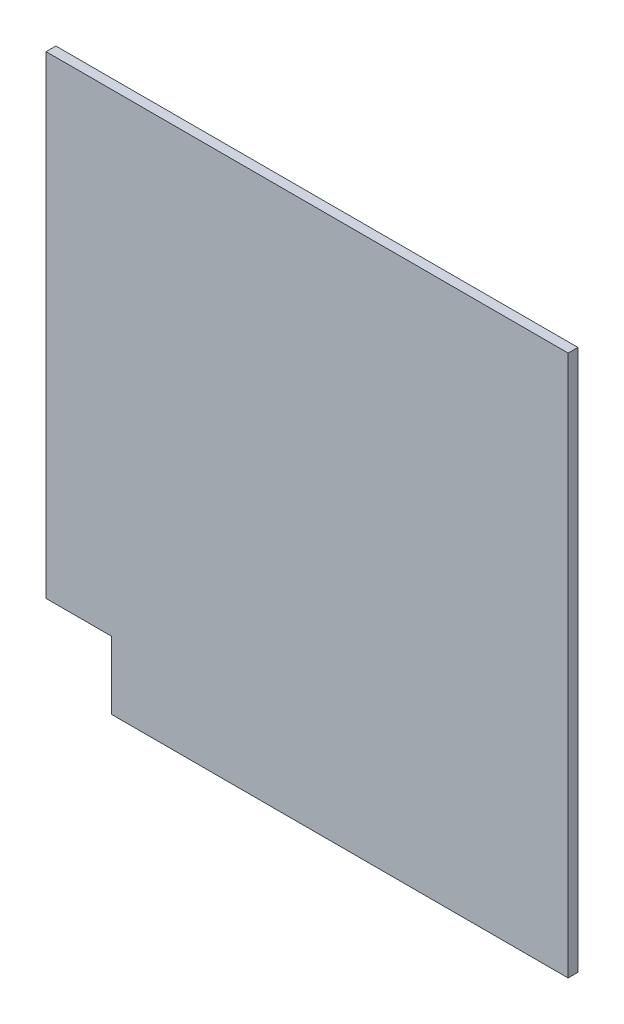
SolidWorks part; units mm, degrees
ref_plane "Front Plane" through (0, 0, 0) normal (0, 0, 1) x (1, 0, 0)
ref_plane "Top Plane" through (0, 0, 0) normal (0, 1, 0) x (1, 0, 0)
ref_plane "Right Plane" through (0, 0, 0) normal (1, 0, 0) x (0, 0, -1)
sketch "Sketch1" plane through (0, 0, 0) normal (0, 0, 1) x (1, 0, 0)
  line L1 (-40, 41.4693) -> (40, 41.4693)
  line L2 (-40, 41.4693) -> (-40, -31.102)
  line L3 (-30, -41.4693) -> (40, -41.4693)
  line L4 (40, 41.4693) -> (40, -41.4693)
  line L5 (-40, 41.4693) -> (40, -41.4693) construction
  line L6 (-30, -31.102) -> (40, 41.4693) construction
  line L9 (-40, -31.102) -> (-30, -31.102)
  line L10 (-30, -41.4693) -> (-30, -31.102)
  point P0 (0, 0)
  dimension "D2" = 82.9386
  dimension "D3" = 10
  dimension "D4" = 10.3673
extrude "Boss-Extrude1" add sketch "Sketch1" along normal blind 1.5
